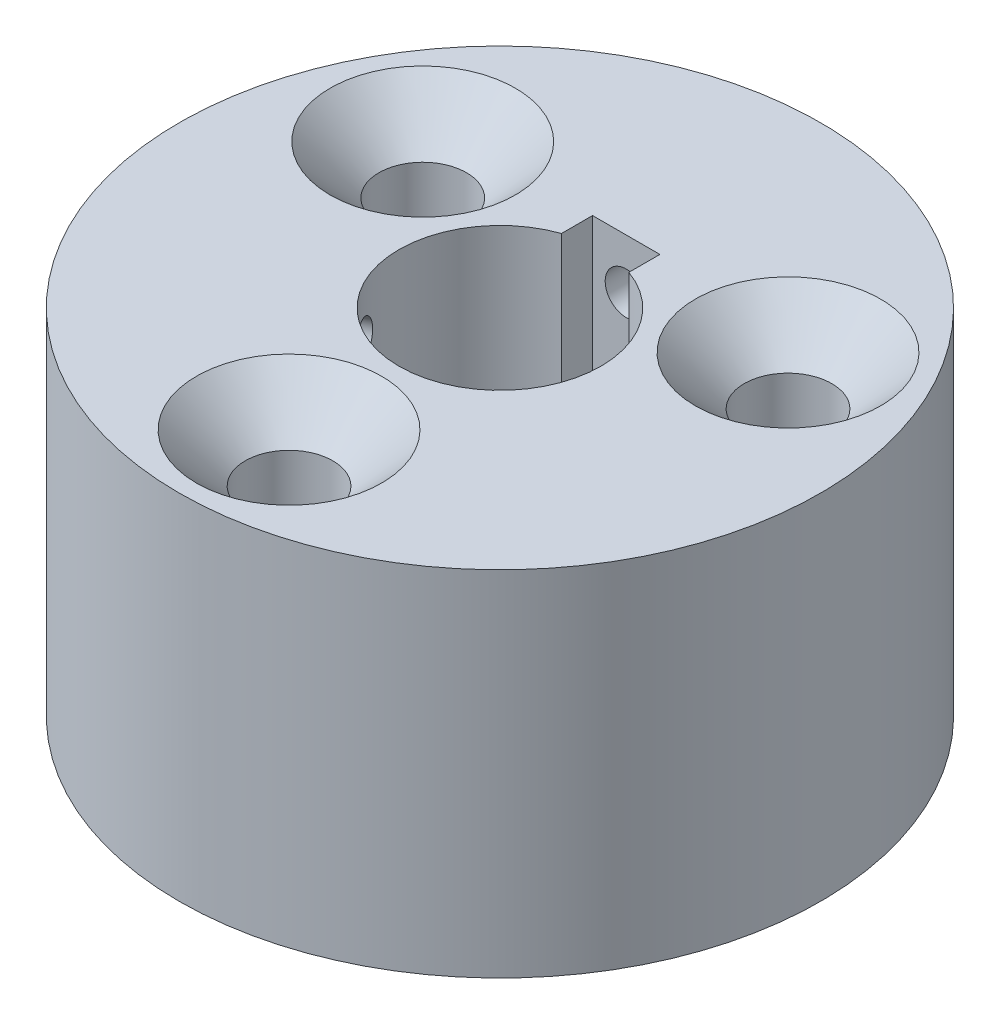
SolidWorks part; units mm, degrees
material "1060 Alloy"
ref_plane "Front Plane" through (0, 0, 0) normal (0, 0, 1) x (1, 0, 0)
ref_plane "Top Plane" through (0, 0, 0) normal (0, 1, 0) x (1, 0, 0)
ref_plane "Right Plane" through (0, 0, 0) normal (1, 0, 0) x (0, 0, -1)
sketch "Sketch1" plane through (0, 0, 0) normal (0, 1, 0) x (1, 0, 0)
  line L0 (0, 6) -> (0, 7.5) construction
  line L1 (-2, 7.5) -> (2, 7.5)
  line L2 (-2, 7.5) -> (-2, 5.6569)
  line L3 (2, 7.5) -> (2, 5.6569)
  line L4 (1, 7.5) -> (-1, 7.5)
  line L6 (0, 0) -> (-10.847, 6.2625) construction
  line L7 (0, 6) -> (0, -6) construction
  line L8 (0, -6) -> (0, -19.05) construction
  line L9 (0, 0) -> (10.847, 6.2625) construction
  circle A0 centre (0, 0) radius 19.05
  circle A1 centre (0, 0) radius 6
  circle A5 centre (0, -12.525) radius 2.5
  circle A6 centre (-10.847, 6.2625) radius 2.5
  circle A7 centre (10.847, 6.2625) radius 2.5
  point P9 (0, 7.5)
  point P16 (0, 7.5)
  dimension "D1" = 12
  dimension "D4" = 1
  dimension "D5" = 38.1
  dimension "D6" = 5
  dimension "D7" = 3
  dimension "D9" = 120
  dimension "D2" = 1.5
  dimension "D3" = 4
  dimension "D8" = 120
extrude "Boss-Extrude1" add sketch "Sketch1" along normal blind 21
sketch "Sketch2" plane through (0, 0, -7.5) normal (0, 0, 1) x (1, 0, 0)
  line L0 (0, 21) -> (0, 0) construction
  line L2 (-2, 21) -> (2, 21) construction
  circle A0 centre (0, 18) radius 1.25
  dimension "D2" = 2.5
  dimension "D1" = 3
extrude "Cut-Extrude1" cut sketch "Sketch2" against normal blind 15 and the other way blind 3
cosmetic thread "Cosmetic Thread2" parameters "D2"=3
ref_plane "Plane1" through (0, 0, 0) normal (-0.866, 0, 0.5) x (0, -1, 0)
sketch "Sketch4" plane through (0, 0, 0) normal (-0.866, 0, 0.5) x (0, -1, 0)
  line L2 (0, 0) -> (-21, 0) construction
  line L3 (0, -19.05) -> (0, 19.05) construction
  line L4 (-21, 19.05) -> (-21, -19.05) construction
  circle A1 centre (-18, 0) radius 1.25
  dimension "D1" = 2.5
  dimension "D2" = 3
  dimension "D3" = 0
extrude "Cut-Extrude2" cut sketch "Sketch4" along normal blind 20
cosmetic thread "Cosmetic Thread3" parameters "D2"=3
ref_plane "Plane3" through (0, 0, -19.05) normal (0, 0, -1) x (-1, 0, 0)
thread "Thread1" pitch 0.5 start angle 0, offset 0, length 0, pitch 0.5, diameter 2.5
ref_plane "Plane4" through (-1.25, 18, -7.5) normal (0, -1, 0) x (-1, 0, 0)
sketch "Thread Profile2" plane through (-1.25, 18, -7.5) normal (0, -1, 0) x (-1, 0, 0)
  line L0 (0, 0) -> (0, 0.5) construction
  line L1 (0, 0) -> (0.2706, 0.1562)
  line L2 (0.2706, 0.1562) -> (0.2706, 0.2187)
  line L3 (0.2706, 0.2187) -> (0, 0.375)
  line L4 (0.2706, 0.1875) -> (0, 0.1875) construction
  line L11 (0, 0) -> (0, 0.375)
  point P2 (0, 0)
  dimension "Pitch" = 0.5
  dimension "Profile_Angle" = 60
  dimension "Profile_Land" = 0.0625
  dimension "Profile_Height" = 0.2706
ref_plane "Plane5" through (-5.1962, 0, 3) normal (0.866, 0, -0.5) x (-0.5, 0, -0.866)
ref_plane "Plane6" through (-16.4978, 0, 9.525) normal (-0.866, 0, 0.5) x (0.5, 0, 0.866)
thread "Thread2" pitch 0.5 start angle 0, offset 0, length 0, pitch 0.5, diameter 2.5
ref_plane "Plane7" through (-4.5712, 18, 4.0825) normal (0, -1, 0) x (0.5, 0, 0.866)
sketch "Thread Profile3" plane through (-4.5712, 18, 4.0825) normal (0, -1, 0) x (0.5, 0, 0.866)
  line L0 (0, 0) -> (0, 0.5) construction
  line L1 (0, 0) -> (0.2706, 0.1562)
  line L2 (0.2706, 0.1562) -> (0.2706, 0.2187)
  line L3 (0.2706, 0.2187) -> (0, 0.375)
  line L4 (0.2706, 0.1875) -> (0, 0.1875) construction
  line L11 (0, 0) -> (0, 0.375)
  point P2 (0, 0)
  dimension "Pitch" = 0.5
  dimension "Profile_Angle" = 60
  dimension "Profile_Land" = 0.0625
  dimension "Profile_Height" = 0.2706
sketch "Sketch18" plane through (0, 21, 0) normal (0, 1, 0) x (1, 0, 0)
  line L0 (0, -6) -> (0, -19.05) construction
  line L1 (-5.1962, 3) -> (-16.4978, 9.525) construction
  line L2 (5.1962, 3) -> (16.4978, 9.525) construction
  arc A0 (-2, 5.6569) -> (2, 5.6569) centre (0, 0) ccw construction
  circle A1 centre (0, 0) radius 19.05 construction
  point P8 (0, -12.525)
  point P13 (-10.847, 6.2625)
  point P16 (10.847, 6.2625)
  point P17 (0, 0)
  dimension "D1" = 3
hole_wizard "CSK for M5 SFHCS1" positions "Sketch18" profile "Sketch19" countersink size "M5" standard "ANSI Metric" end condition through all
sketch "Sketch19" plane through (10.847, 21, -6.2625) normal (1, 0, 0) x (0, 0, 1)
  line L0 (0, 0) -> (0, 21)
  line L1 (0, 21) -> (2.6, 21)
  line L2 (2.6, 21) -> (2.6, 2.9)
  line L3 (2.6, 2.9) -> (5.5, 0)
  line L5 (5.5, 0) -> (0, 0)
  line L6 (-2.6, 2.9) -> (-5.5, 0) construction
  line L11 (0, -6.35) -> (0, 107.95) construction
  dimension "Thru Hole Dia." = 5.2
  dimension "Thru Hole Depth" = 21
  dimension "Near C'Sink Dia." = 11
  dimension "Near C'Sink Angle" = 90
